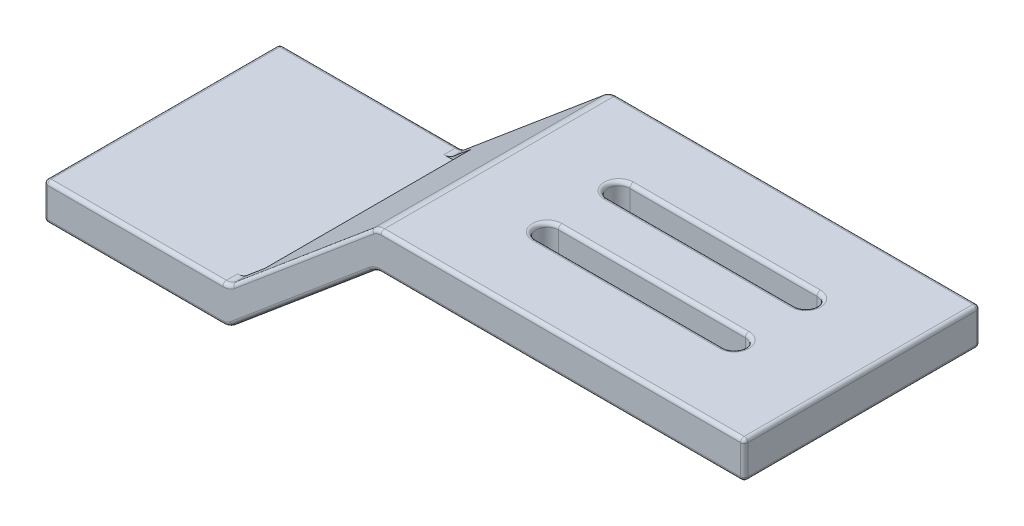
SolidWorks part; units mm, degrees
ref_plane "前视基准面" through (0, 0, 0) normal (0, 0, 1) x (1, 0, 0)
ref_plane "上视基准面" through (0, 0, 0) normal (0, 1, 0) x (1, 0, 0)
ref_plane "右视基准面" through (0, 0, 0) normal (1, 0, 0) x (0, 0, -1)
sketch "草图1" plane through (0, 0, 0) normal (0, 0, 1) x (1, 0, 0)
  line L1 (0, 0) -> (25, 0)
  line L2 (0, 0) -> (0, 5)
  line L3 (0, 5) -> (25, 5)
  line L4 (25, 0) -> (25, 5)
  line L5 (0, 0) -> (25, 5) construction
  line L6 (0, 5) -> (25, 0) construction
  point P4 (12.5, 2.5)
  dimension "D1" = 25
  dimension "D2" = 5
extrude "凸台-拉伸1" add sketch "草图1" along normal blind 32
sketch "草图2" plane through (0, 0, 32) normal (0, 0, 1) x (1, 0, 0)
  line L0 (25, 0) -> (25, 5)
  line L1 (25, 0) -> (45, 16.782)
  line L2 (25, 5) -> (45, 21.782)
  line L3 (45, 16.782) -> (45, 21.782)
  line L4 (25, 0) -> (25, 5) construction
  line L6 (45, 16.782) -> (95, 16.782)
  line L7 (45, 16.782) -> (45, 21.782)
  line L8 (45, 21.782) -> (95, 21.782)
  line L9 (95, 16.782) -> (95, 21.782)
  line L10 (45, 16.782) -> (95, 21.782) construction
  line L11 (45, 21.782) -> (95, 16.782) construction
  point P3 (0, 0)
  point P10 (70, 19.282)
  point P11 (0, 0)
  line M10 (25, 0) -> (25, 5)
  dimension "D1" = 140
  dimension "D2" = 50
  dimension "D3" = 20
extrude "凸台-拉伸2" add sketch "草图2" against normal up to surface (32 mm away) contours L1 L3 L2 M10 | L6 L9 L8 L3 up to face at (12.5, 2.5, 0)
fillet "圆角1" radius 2 4 edges at (45, 21.782, 16) (25, 5, 16) (45, 16.782, 16) (25, 0, 16)
extrude "切除-拉伸1" cut sketch "草图3" against normal blind 10
sketch "草图3" plane through (152.0637, 21.782, 93.1244) normal (0, 1, 0) x (0, 0, -1)
  line L4 (70.7689, 94.93) -> (70.7689, 69.5637)
  line L5 (73.7689, 69.5637) -> (73.7689, 94.93)
  line L6 (83.4799, 69.5637) -> (83.4799, 94.93)
  line L7 (80.4799, 94.93) -> (80.4799, 69.5637)
  arc A4 (70.7689, 69.5637) -> (73.7689, 69.5637) centre (72.2689, 69.5637) ccw
  arc A5 (73.7689, 94.93) -> (70.7689, 94.93) centre (72.2689, 94.93) ccw
  arc A6 (80.4799, 69.5637) -> (83.4799, 69.5637) centre (81.9799, 69.5637) ccw
  arc A7 (83.4799, 94.93) -> (80.4799, 94.93) centre (81.9799, 94.93) ccw
fillet "圆角2" radius 0.5 44 edges at (45.0439, 16.6614, 0) (45.0439, 16.6614, 32) (24.9561, 5.1206, 32) (24.9561, 5.1206, 0) (45.0439, 21.6614, 0) (24.9561, 0.1206, 0) (45.0439, 21.6614, 32) (24.9561, 0.1206, 32) (0, 0, 16) (0, 5, 16) (12.136, 5, 32) (12.136, 5, 0) (12.136, 0, 0) (12.136, 0, 32) (0, 2.5, 0) (0, 2.5, 32) (35, 8.391, 0) (35, 8.391, 32) (35, 13.391, 32) (70.364, 21.782, 32) (95, 21.782, 16) (95, 19.282, 0) (95, 19.282, 32) (95, 16.782, 16) (70.364, 16.782, 32) (70.364, 16.782, 0) (70.364, 21.782, 0) (35, 13.391, 0) (84, 16.782, 20.8555) (69.8169, 16.782, 22.3555) (55.6337, 16.782, 20.8555) (69.8169, 16.782, 19.3555) (84, 16.782, 11.1445) (69.8169, 16.782, 12.6445) (55.6337, 16.782, 11.1445) (69.8169, 16.782, 9.6445) (69.8169, 21.782, 22.3555) (55.6337, 21.782, 20.8555) (69.8169, 21.782, 19.3555) (84, 21.782, 20.8555) (69.8169, 21.782, 12.6445) (55.6337, 21.782, 11.1445) (69.8169, 21.782, 9.6445) (84, 21.782, 11.1445)
sketch "草图4" plane through (0, 5, 0) normal (0, 1, 0) x (1, 0, 0)
  line L0 (0, -31.5) -> (0, -0.5) construction
  line L1 (0, -2) -> (28, -2)
  line L2 (0, -2) -> (0, -30)
  line L3 (0, -30) -> (28, -30)
  line L4 (28, -2) -> (28, -30)
  line L5 (0, -2) -> (28, -30) construction
  line L6 (0, -30) -> (28, -2) construction
  line L7 (25.5576, -16) -> (14, -16) construction
  line L8 (25.5576, -0.5) -> (25.5576, -31.5) construction
  point P4 (14, -16)
  dimension "D1" = 28
extrude "切除-拉伸2" cut sketch "草图4" along normal blind 10
